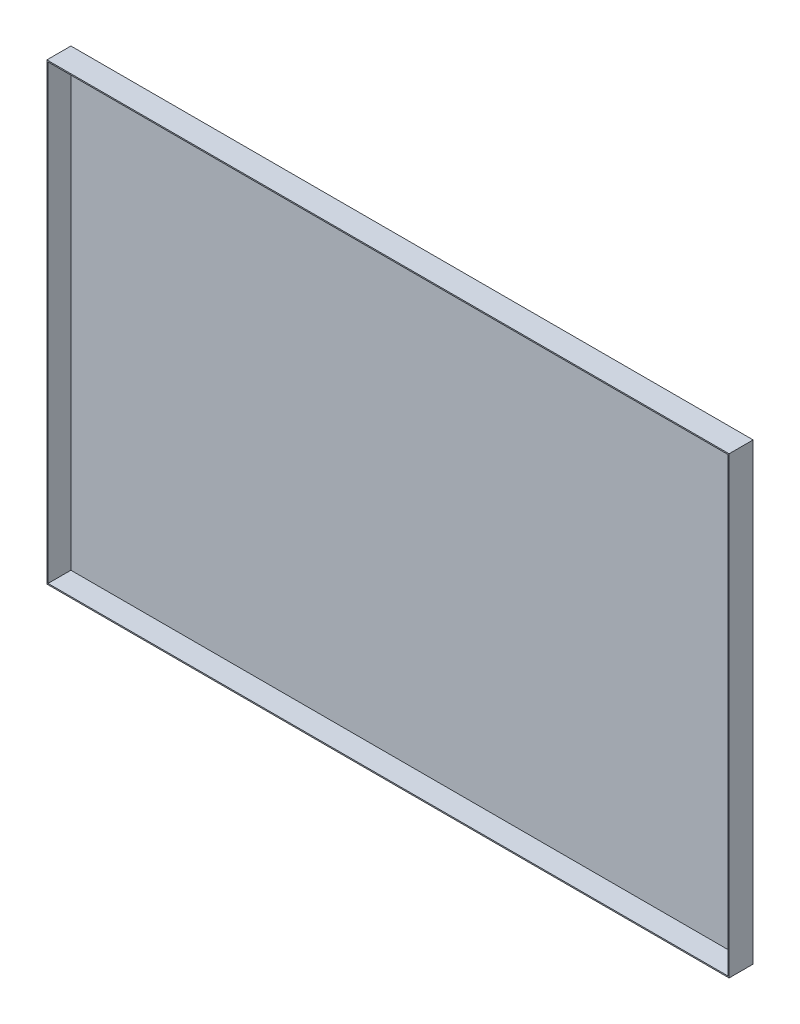
SolidWorks part; units mm, degrees
ref_plane "前视基准面" through (0, 0, 0) normal (0, 0, 1) x (1, 0, 0)
ref_plane "上视基准面" through (0, 0, 0) normal (0, 1, 0) x (1, 0, 0)
ref_plane "右视基准面" through (0, 0, 0) normal (1, 0, 0) x (0, 0, -1)
sketch "草图1" plane through (0, 0, 0) normal (0, 0, 1) x (1, 0, 0)
  line L1 (-284, 189) -> (284, 189)
  line L2 (-284, 189) -> (-284, -189)
  line L3 (-284, -189) -> (284, -189)
  line L4 (284, 189) -> (284, -189)
  line L5 (-284, 189) -> (284, -189) construction
  line L6 (-284, -189) -> (284, 189) construction
  point P0 (0, 0)
  dimension "D1" = 568
  dimension "D2" = 378
extrude "凸台-拉伸1" add sketch "草图1" along normal blind 20
shell "抽壳1" thickness 1
